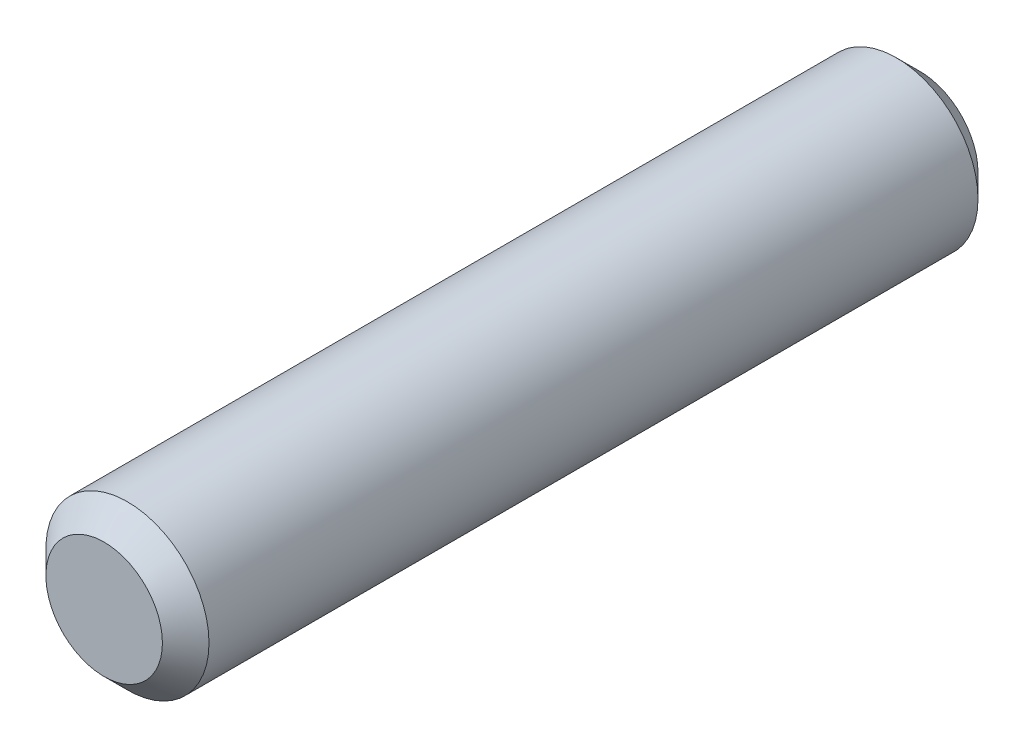
SolidWorks part; units mm, degrees
ref_plane "Front Plane" through (0, 0, 0) normal (0, 0, 1) x (1, 0, 0)
ref_plane "Top Plane" through (0, 0, 0) normal (0, 1, 0) x (1, 0, 0)
ref_plane "Right Plane" through (0, 0, 0) normal (1, 0, 0) x (0, 0, -1)
sketch "Sketch2" plane through (0, 0, 0) normal (0, 0, 1) x (1, 0, 0)
  circle A0 centre (0, 0) radius 7
  dimension "D1" = 14
extrude "Boss-Extrude1" add sketch "Sketch2" along normal mid plane 70
chamfer "Chamfer1" distance 2 angle 45 1 edges at (7, 0, -35)
chamfer "Chamfer2" distance 2 angle 45 1 edges at (7, 0, 35)
